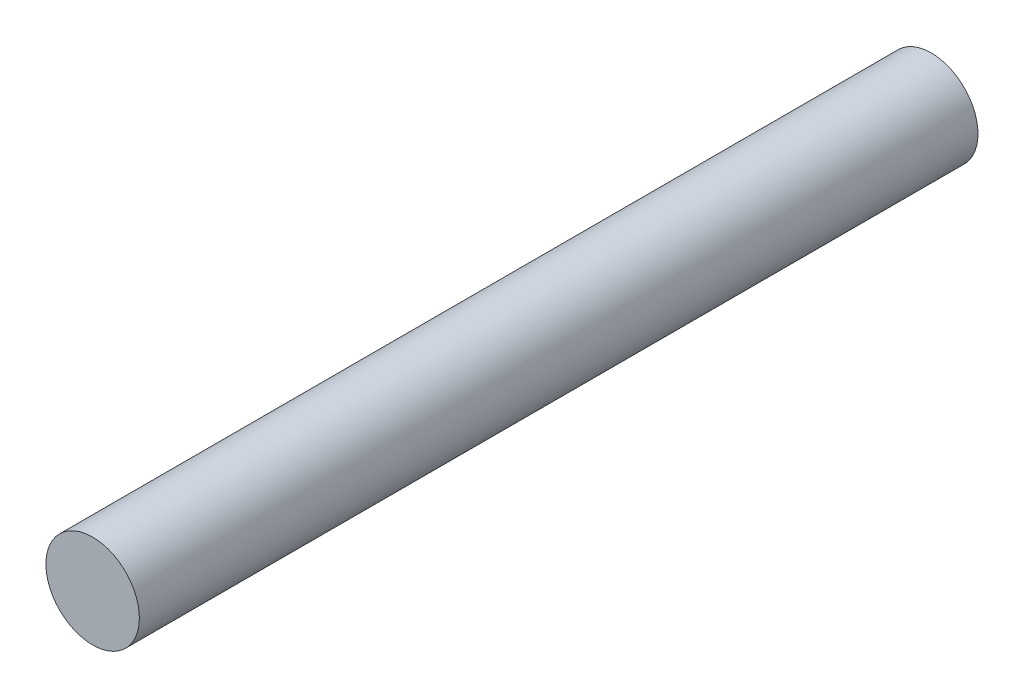
SolidWorks part; units mm, degrees
ref_plane "정면" through (0, 0, 0) normal (0, 0, 1) x (1, 0, 0)
ref_plane "윗면" through (0, 0, 0) normal (0, 1, 0) x (1, 0, 0)
ref_plane "우측면" through (0, 0, 0) normal (1, 0, 0) x (0, 0, -1)
sketch "스케치1" plane through (0, 0, 0) normal (0, 0, 1) x (1, 0, 0)
  circle A0 centre (0, 0) radius 1.95
  dimension "D1" = 3.9
extrude "보스-돌출1" add sketch "스케치1" along normal blind 35 contours A0
